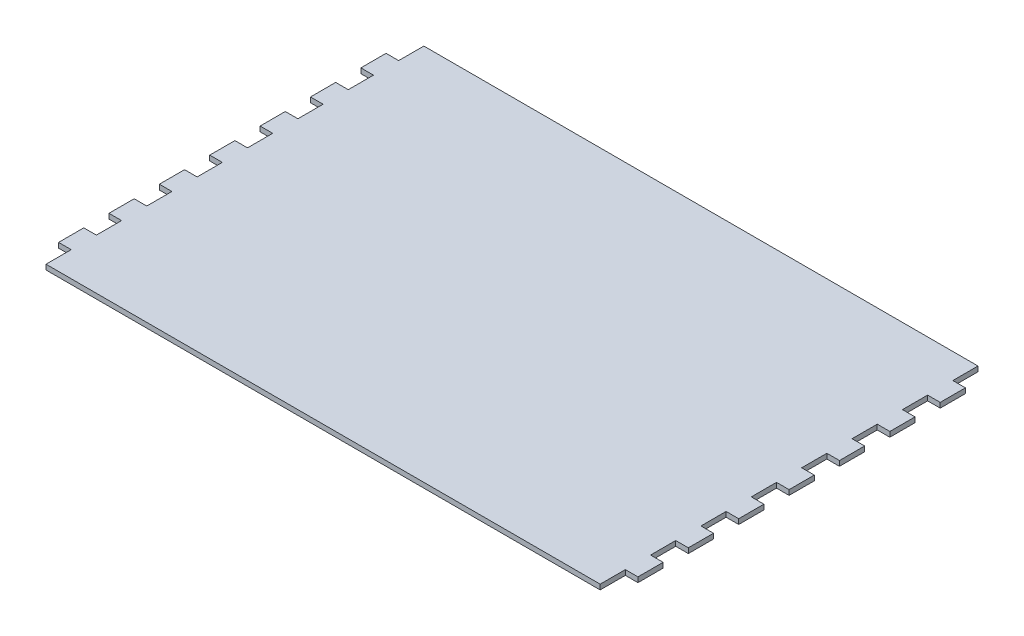
SolidWorks part; units mm, degrees
ref_plane "Front Plane" through (0, 0, 0) normal (0, 0, 1) x (1, 0, 0)
ref_plane "Top Plane" through (0, 0, 0) normal (0, 1, 0) x (1, 0, 0)
ref_plane "Right Plane" through (0, 0, 0) normal (1, 0, 0) x (0, 0, -1)
sketch "Sketch1" plane through (0, 0, 0) normal (0, 1, 0) x (1, 0, 0)
  line L0 (0, 0) -> (279.4, 0)
  line L1 (0, 0) -> (0, -12.7)
  line L2 (0, -12.7) -> (-6.35, -12.7)
  line L3 (-6.35, -12.7) -> (-6.35, -25.4)
  line L4 (-6.35, -25.4) -> (0, -25.4)
  line L5 (0, -25.4) -> (0, -38.1)
  line L6 (0, -38.1) -> (-6.35, -38.1)
  line L7 (-6.35, -38.1) -> (-6.35, -50.8)
  line L8 (-6.35, -50.8) -> (0, -50.8)
  line L9 (0, -50.8) -> (0, -63.5)
  line L10 (0, -63.5) -> (-6.35, -63.5)
  line L11 (-6.35, -63.5) -> (-6.35, -76.2)
  line L12 (-6.35, -76.2) -> (0, -76.2)
  line L13 (0, -76.2) -> (0, -88.9)
  line L14 (0, -88.9) -> (-6.35, -88.9)
  line L15 (-6.35, -88.9) -> (-6.35, -101.6)
  line L16 (-6.35, -101.6) -> (0, -101.6)
  line L17 (0, -101.6) -> (0, -114.3)
  line L18 (0, -114.3) -> (-6.35, -114.3)
  line L19 (-6.35, -114.3) -> (-6.35, -127)
  line L20 (-6.35, -127) -> (0, -127)
  line L21 (0, -127) -> (0, -139.7)
  line L22 (0, -139.7) -> (-6.35, -139.7)
  line L23 (-6.35, -139.7) -> (-6.35, -152.4)
  line L24 (-6.35, -152.4) -> (0, -152.4)
  line L25 (0, -152.4) -> (0, -165.1)
  line L26 (139.7, 0) -> (139.7, -165.1) construction
  line L27 (0, -165.1) -> (-6.35, -165.1)
  line L28 (-6.35, -165.1) -> (-6.35, -177.8)
  line L29 (-6.35, -177.8) -> (0, -177.8)
  line L30 (0, -177.8) -> (0, -190.5)
  line L31 (279.4, -177.8) -> (279.4, -190.5)
  line L32 (285.75, -177.8) -> (279.4, -177.8)
  line L33 (285.75, -165.1) -> (285.75, -177.8)
  line L34 (279.4, -165.1) -> (285.75, -165.1)
  line L35 (279.4, -152.4) -> (279.4, -165.1)
  line L36 (285.75, -152.4) -> (279.4, -152.4)
  line L37 (285.75, -139.7) -> (285.75, -152.4)
  line L38 (279.4, -139.7) -> (285.75, -139.7)
  line L39 (279.4, -127) -> (279.4, -139.7)
  line L40 (285.75, -127) -> (279.4, -127)
  line L41 (285.75, -114.3) -> (285.75, -127)
  line L42 (279.4, -114.3) -> (285.75, -114.3)
  line L43 (279.4, -101.6) -> (279.4, -114.3)
  line L44 (285.75, -101.6) -> (279.4, -101.6)
  line L45 (285.75, -88.9) -> (285.75, -101.6)
  line L46 (279.4, -88.9) -> (285.75, -88.9)
  line L47 (279.4, -76.2) -> (279.4, -88.9)
  line L48 (285.75, -76.2) -> (279.4, -76.2)
  line L49 (285.75, -63.5) -> (285.75, -76.2)
  line L50 (279.4, -63.5) -> (285.75, -63.5)
  line L51 (279.4, -50.8) -> (279.4, -63.5)
  line L52 (285.75, -50.8) -> (279.4, -50.8)
  line L53 (285.75, -38.1) -> (285.75, -50.8)
  line L54 (279.4, -38.1) -> (285.75, -38.1)
  line L55 (279.4, -25.4) -> (279.4, -38.1)
  line L56 (285.75, -25.4) -> (279.4, -25.4)
  line L57 (285.75, -12.7) -> (285.75, -25.4)
  line L58 (279.4, -12.7) -> (285.75, -12.7)
  line L59 (279.4, 0) -> (279.4, -12.7)
  line L60 (0, -190.5) -> (279.4, -190.5)
  dimension "D1" = 12.7
  dimension "D2" = 12.7
  dimension "D3" = 6.35
  dimension "D4" = 6.35
  dimension "D5" = 279.4
  dimension "D7" = 12.7
  dimension "D6" = 7
extrude "Boss-Extrude1" add sketch "Sketch1" along normal blind 2.54
